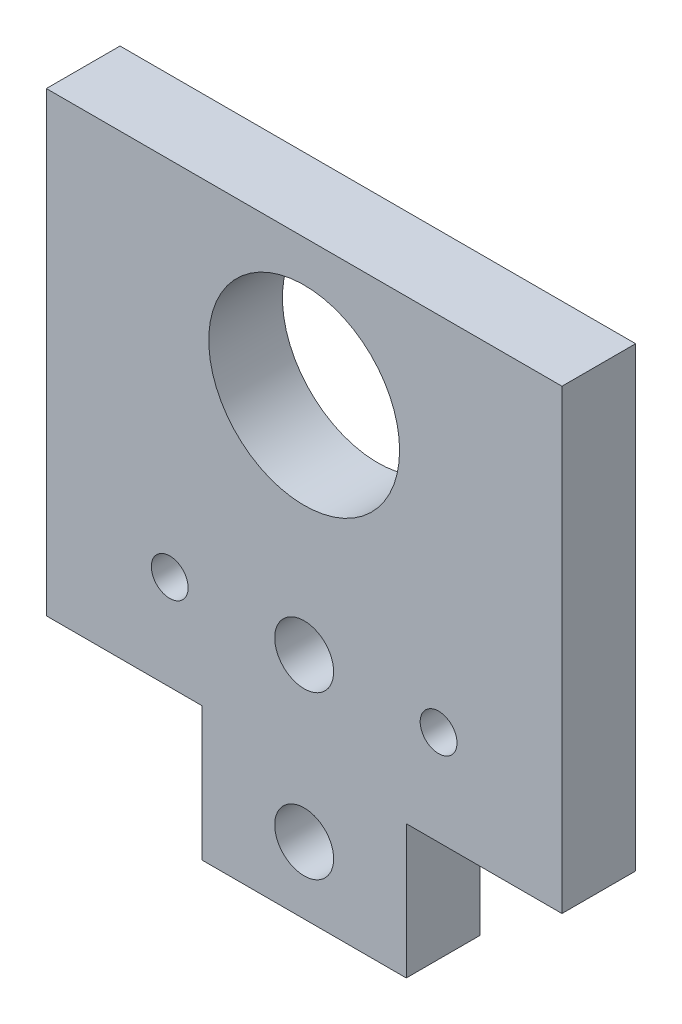
SolidWorks part; units mm, degrees
ref_plane "Front Plane" through (0, 0, 0) normal (0, 0, 1) x (1, 0, 0)
ref_plane "Top Plane" through (0, 0, 0) normal (0, 1, 0) x (1, 0, 0)
ref_plane "Right Plane" through (0, 0, 0) normal (1, 0, 0) x (0, 0, -1)
sketch "Sketch1" plane through (0, 0, 0) normal (0, 0, 1) x (1, 0, 0)
  line L0 (0, 40.0739) -> (0, -40.0739) construction
  line L1 (-35, 40.0739) -> (35, 40.0739)
  line L2 (35, 40.0739) -> (35, -21.9261)
  line L3 (35, -21.9261) -> (13.8611, -21.9261)
  line L4 (13.8611, -21.9261) -> (13.8611, -40.0739)
  line L5 (13.8611, -40.0739) -> (-13.8611, -40.0739)
  line L6 (-13.8611, -21.9261) -> (-13.8611, -40.0739)
  line L7 (-35, -21.9261) -> (-13.8611, -21.9261)
  line L8 (-35, 40.0739) -> (-35, -21.9261)
  dimension "D1" = 70
  dimension "D2" = 27.7222
  dimension "D3" = 18.1478
  dimension "D4" = 62
extrude "Boss-Extrude1" add sketch "Sketch1" along normal blind 10
sketch "Sketch2" plane through (0, 0, 10) normal (0, 0, 1) x (1, 0, 0)
  line L0 (0, 40.0739) -> (0, -40.0739) construction
  line L1 (35, 40.0739) -> (-35, 40.0739) construction
  line L2 (-13.8611, -40.0739) -> (13.8611, -40.0739) construction
  line L3 (-13.8611, -31) -> (13.8611, -31) construction
  line L4 (-13.8611, -21.9261) -> (-13.8611, -40.0739) construction
  line L5 (13.8611, -40.0739) -> (13.8611, -21.9261) construction
  line L6 (-35, 0) -> (35, 0) construction
  line L7 (-35, 40.0739) -> (-35, -21.9261) construction
  line L8 (35, -21.9261) -> (35, 40.0739) construction
  line L9 (-35, 32.3714) -> (35, 32.3714) construction
  line L11 (-35, -21.9261) -> (-13.8611, -21.9261) construction
  line L12 (-35, -9) -> (35, -9) construction
  circle A0 centre (0, -31) radius 4
  circle A1 centre (0, -9) radius 4
  circle A2 centre (-18.25, -9) radius 2.5
  circle A3 centre (18.25, -9) radius 2.5
  point P29 (-18.25, -9)
  point P30 (18.25, -9)
  dimension "D1" = 8
  dimension "D2" = 8
  dimension "D3" = 22
  dimension "D4" = 12.9261
  dimension "D7" = 5
  dimension "D5" = 18.25
  dimension "D6" = 18.25
extrude "Cut-Extrude1" cut sketch "Sketch2" against normal through all
sketch "Sketch8" plane through (0, 0, 10) normal (0, 0, 1) x (1, 0, 0)
  line L0 (0, 40.0739) -> (0, -5) construction
  line L1 (35, 40.0739) -> (-35, 40.0739) construction
  circle A0 centre (0, -9) radius 4 construction
  circle A1 centre (0, 21.5139) radius 12.955
  dimension "D1" = 25.91
  dimension "D2" = 18.56
extrude "Cut-Extrude9" cut sketch "Sketch8" against normal blind 10 contours A1
